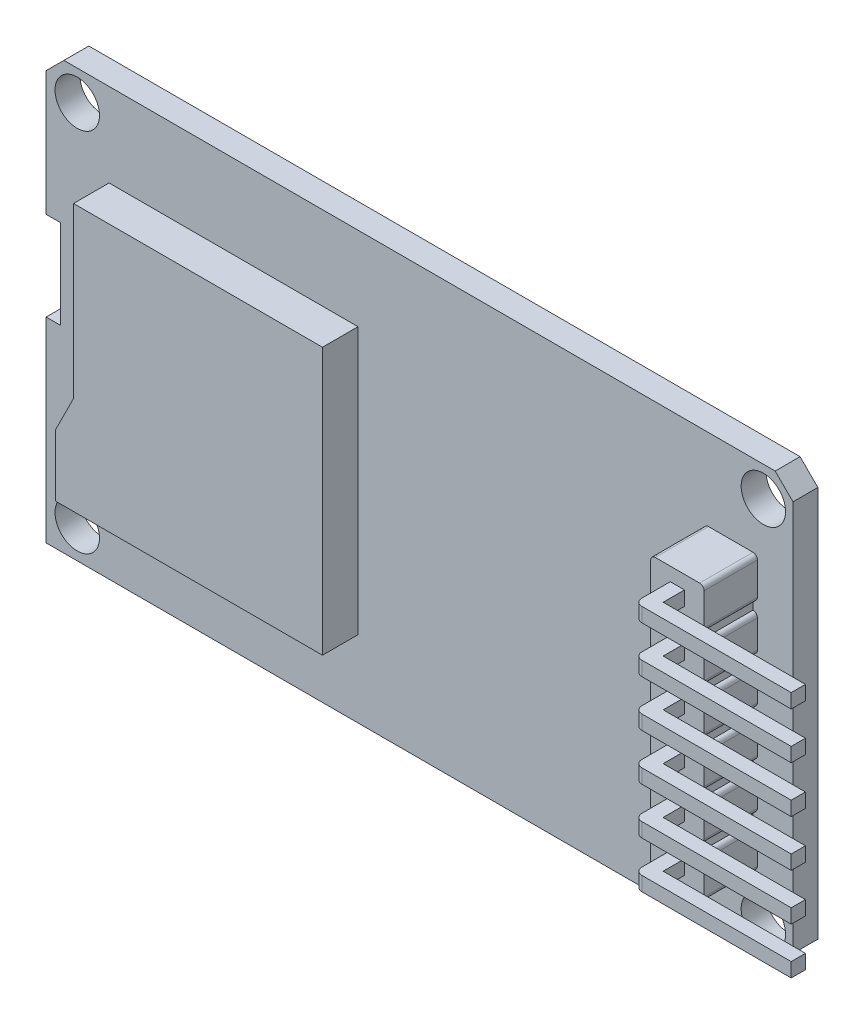
SolidWorks part; units mm, degrees
ref_plane "Front Plane" through (0, 0, 0) normal (0, 0, 1) x (1, 0, 0)
ref_plane "Top Plane" through (0, 0, 0) normal (0, 1, 0) x (1, 0, 0)
ref_plane "Right Plane" through (0, 0, 0) normal (1, 0, 0) x (0, 0, -1)
sketch "Sketch1" plane through (0, 0, 0) normal (0, 0, 1) x (1, 0, 0)
  line L0 (-17.6235, 12) -> (-16.6235, 13)
  line L1 (-17.6235, -11) -> (23.3765, -11)
  line L3 (-16.6235, 13) -> (23.3765, 13)
  line L4 (24.3765, -10) -> (24.3765, 12)
  line L5 (23.3765, 13) -> (24.3765, 12)
  line L6 (23.3765, -11) -> (24.3765, -10)
  line L7 (-17.6235, 0) -> (-16.8235, 0)
  line L8 (-16.8235, 0) -> (-16.8235, 5)
  line L9 (-16.8235, 5) -> (-17.6235, 5)
  line L10 (-17.6235, 5) -> (-17.6235, 12)
  line L11 (-17.6235, 0) -> (-17.6235, -11)
  point P1 (24.3765, 13)
  point P2 (-17.6235, 13)
  point P3 (24.3765, -11)
  dimension "D1" = 42
  dimension "D2" = 24
  dimension "D3" = 11
  dimension "D4" = 5
  dimension "D8" = 0.8
extrude "Boss-Extrude1" add sketch "Sketch1" along normal blind 1.4 contours L0 L3 L5 L4 L6 L1 L11 L7 L8 L9 L10
hole_wizard "Ø2.5 (2.5) Diameter Slot1" positions "Sketch4" profile "Sketch5" size "Ø2.5" standard "ISO" slot yes end condition through all
sketch "Sketch4" plane through (0, 0, 1.4) normal (0, 0, 1) x (1, 0, 0)
  point P0 (-15.8743, -9.2692)
  point P2 (-15.8743, 11.3127)
  point P4 (22.7108, -9.2692)
  point P6 (22.7108, 11.3127)
sketch "Sketch5" plane through (-15.8743, -9.2692, 1.4) normal (1, 0, 0) x (0, -1, 0)
  line L0 (0, 0) -> (0, 1.4)
  line L1 (0, 1.4) -> (1.25, 1.4)
  line L2 (1.25, 1.4) -> (1.25, 0)
  line L5 (1.25, 0) -> (0, 0)
  line L11 (0, -6.35) -> (0, 15.6736) construction
  dimension "Thru Hole Dia." = 2.5
  dimension "Thru Hole Depth" = 1.4
sketch "Sketch6" plane through (0, 0, 1.4) normal (0, 0, 1) x (1, 0, 0)
  line L0 (-15.0835, -6.7) -> (-0.0835, -6.7)
  line L1 (-17.6235, -11) -> (23.3765, -11) construction
  line L2 (-17.6235, 0) -> (-17.6235, -11) construction
  line L3 (-0.0835, -6.7) -> (-0.0835, 8.3)
  line L4 (-0.0835, 8.3) -> (-14.0835, 8.3)
  line L5 (-14.0835, 8.3) -> (-14.0835, -1.2)
  line L6 (-14.0835, -1.2) -> (-15.0835, -3.2)
  line L7 (-15.0835, -3.2) -> (-15.0835, -6.7)
  dimension "D1" = 4.3
  dimension "D2" = 15
  dimension "D3" = 2.54
  dimension "D4" = 15
  dimension "D5" = 14
  dimension "D6" = 3.5
  dimension "D7" = 9.5
extrude "Boss-Extrude2" add sketch "Sketch6" along normal blind 2
sketch "Sketch7" plane through (0, 0, 1.4) normal (0, 0, 1) x (1, 0, 0)
  line L0 (22.1265, 6.1) -> (22.1265, 5.6)
  line L1 (22.1265, 8.42) -> (19.6265, 8.42)
  line L2 (19.6265, 6.1) -> (19.6265, 5.6)
  line L3 (22.1265, -7) -> (19.6265, -7)
  line L4 (19.6265, 3.53) -> (19.6265, 3.03)
  line L5 (-17.6235, -11) -> (23.3765, -11) construction
  line L6 (22.3765, 8.17) -> (22.3765, 6.35)
  line L7 (19.3765, 8.17) -> (19.3765, 6.35)
  line L8 (19.3765, 5.35) -> (19.3765, 3.78)
  line L9 (22.3765, 5.35) -> (22.3765, 3.78)
  line L10 (22.3765, 2.78) -> (22.3765, 1.21)
  line L11 (22.1265, -1.61) -> (22.1265, -2.11)
  line L12 (19.6265, -1.61) -> (19.6265, -2.11)
  line L13 (22.1265, -4.18) -> (22.1265, -4.68)
  line L14 (19.6265, -4.68) -> (19.6265, -4.18)
  line L21 (19.3765, 2.78) -> (19.3765, 1.21)
  line L22 (19.3765, 0.21) -> (19.3765, -1.36)
  line L23 (22.3765, 0.21) -> (22.3765, -1.36)
  line L24 (22.3765, -2.36) -> (22.3765, -3.93)
  line L25 (19.3765, -2.36) -> (19.3765, -3.93)
  line L26 (19.3765, -4.93) -> (19.3765, -6.75)
  line L27 (22.3765, -4.93) -> (22.3765, -6.75)
  line L28 (22.1265, 3.53) -> (22.1265, 3.03)
  line L29 (22.1265, 0.96) -> (22.1265, 0.46)
  line L30 (19.6265, 0.96) -> (19.6265, 0.46)
  arc A0 (22.3765, -6.75) -> (22.1265, -7) centre (22.1265, -6.75) cw
  arc A1 (19.6265, -7) -> (19.3765, -6.75) centre (19.6265, -6.75) cw
  arc A2 (19.6265, -4.68) -> (19.3765, -4.93) centre (19.6265, -4.93) ccw
  arc A3 (22.1265, -4.68) -> (22.3765, -4.93) centre (22.1265, -4.93) cw
  arc A4 (19.6265, -4.18) -> (19.3765, -3.93) centre (19.6265, -3.93) cw
  arc A5 (22.1265, -4.18) -> (22.3765, -3.93) centre (22.1265, -3.93) ccw
  arc A6 (22.1265, -2.11) -> (22.3765, -2.36) centre (22.1265, -2.36) cw
  arc A7 (19.6265, -2.11) -> (19.3765, -2.36) centre (19.6265, -2.36) ccw
  arc A8 (19.6265, -1.61) -> (19.3765, -1.36) centre (19.6265, -1.36) cw
  arc A9 (22.1265, -1.61) -> (22.3765, -1.36) centre (22.1265, -1.36) ccw
  arc A10 (22.1265, 0.46) -> (22.3765, 0.21) centre (22.1265, 0.21) cw
  arc A11 (19.6265, 0.46) -> (19.3765, 0.21) centre (19.6265, 0.21) ccw
  arc A12 (19.6265, 0.96) -> (19.3765, 1.21) centre (19.6265, 1.21) cw
  arc A13 (22.1265, 0.96) -> (22.3765, 1.21) centre (22.1265, 1.21) ccw
  arc A14 (19.6265, 3.03) -> (19.3765, 2.78) centre (19.6265, 2.78) ccw
  arc A15 (22.1265, 3.03) -> (22.3765, 2.78) centre (22.1265, 2.78) cw
  arc A16 (22.1265, 3.53) -> (22.3765, 3.78) centre (22.1265, 3.78) ccw
  arc A17 (19.6265, 3.53) -> (19.3765, 3.78) centre (19.6265, 3.78) cw
  arc A18 (19.3765, 5.35) -> (19.6265, 5.6) centre (19.6265, 5.35) cw
  arc A19 (22.1265, 5.6) -> (22.3765, 5.35) centre (22.1265, 5.35) cw
  arc A20 (22.1265, 6.1) -> (22.3765, 6.35) centre (22.1265, 6.35) ccw
  arc A21 (19.6265, 6.1) -> (19.3765, 6.35) centre (19.6265, 6.35) cw
  arc A22 (19.6265, 8.42) -> (19.3765, 8.17) centre (19.6265, 8.17) ccw
  arc A23 (22.1265, 8.42) -> (22.3765, 8.17) centre (22.1265, 8.17) cw
  point P11 (19.3765, -7)
  point P73 (19.3765, 8.42)
  point P76 (22.3765, 8.42)
  dimension "D1" = 0.25
  dimension "D2" = 3
  dimension "D3" = 15.42
  dimension "D4" = 4
extrude "Boss-Extrude3" add sketch "Sketch7" along normal blind 3
sketch "Sketch8" plane through (0, 0, 4.4) normal (0, 0, 1) x (1, 0, 0)
  line L1 (20.4765, -5.44) -> (21.2765, -5.44)
  line L2 (20.4765, -5.44) -> (20.4765, -6.24)
  line L3 (20.4765, -6.24) -> (21.2765, -6.24)
  line L4 (21.2765, -5.44) -> (21.2765, -6.24)
  line L5 (20.4765, -5.44) -> (21.2765, -6.24) construction
  line L6 (20.4765, -6.24) -> (21.2765, -5.44) construction
  line L8 (21.2765, -2.82) -> (21.2765, -3.62)
  line L9 (20.4765, -2.82) -> (21.2765, -2.82)
  line L10 (20.4765, -2.82) -> (20.4765, -3.62)
  line L11 (20.4765, -3.62) -> (21.2765, -3.62)
  line L12 (21.2765, -0.2) -> (21.2765, -1)
  line L13 (20.4765, -0.2) -> (21.2765, -0.2)
  line L14 (20.4765, -0.2) -> (20.4765, -1)
  line L15 (20.4765, -1) -> (21.2765, -1)
  line L16 (21.2765, 2.42) -> (21.2765, 1.62)
  line L17 (20.4765, 2.42) -> (21.2765, 2.42)
  line L18 (20.4765, 2.42) -> (20.4765, 1.62)
  line L19 (20.4765, 1.62) -> (21.2765, 1.62)
  line L20 (21.2765, 5.04) -> (21.2765, 4.24)
  line L21 (20.4765, 5.04) -> (21.2765, 5.04)
  line L22 (20.4765, 5.04) -> (20.4765, 4.24)
  line L23 (20.4765, 4.24) -> (21.2765, 4.24)
  line L24 (21.2765, 7.66) -> (21.2765, 6.86)
  line L25 (20.4765, 7.66) -> (21.2765, 7.66)
  line L26 (20.4765, 7.66) -> (20.4765, 6.86)
  line L27 (20.4765, 6.86) -> (21.2765, 6.86)
  point P0 (20.8765, -5.84)
  dimension "D1" = 0.8
  dimension "D2" = 0.8
  dimension "D3" = 6
extrude "Boss-Extrude4" add sketch "Sketch8" along normal blind 2
sketch "Sketch9" plane through (21.2765, 0, 0) normal (1, 0, 0) x (0, 0, -1)
  line L0 (-6.4, 7.66) -> (-6.4, 6.86)
  line L1 (-6.4, 7.66) -> (-5.6, 7.66)
  line L2 (-6.4, 6.86) -> (-5.6, 6.86)
  line L3 (-5.6, 7.66) -> (-5.6, 6.86)
  dimension "D1" = 0.8
extrude "Boss-Extrude5" add sketch "Sketch9" along normal blind 8
pattern_linear "LPattern1" count 6 spacing 2.62 along (0, -1, 0) of "Boss-Extrude5"
fillet "Fillet1" radius 0.4 6 edges at (20.4765, 7.26, 6.4) (20.4765, 4.64, 6.4) (20.4765, 2.02, 6.4) (20.4765, -0.6, 6.4) (20.4765, -3.22, 6.4) (20.4765, -5.84, 6.4)
